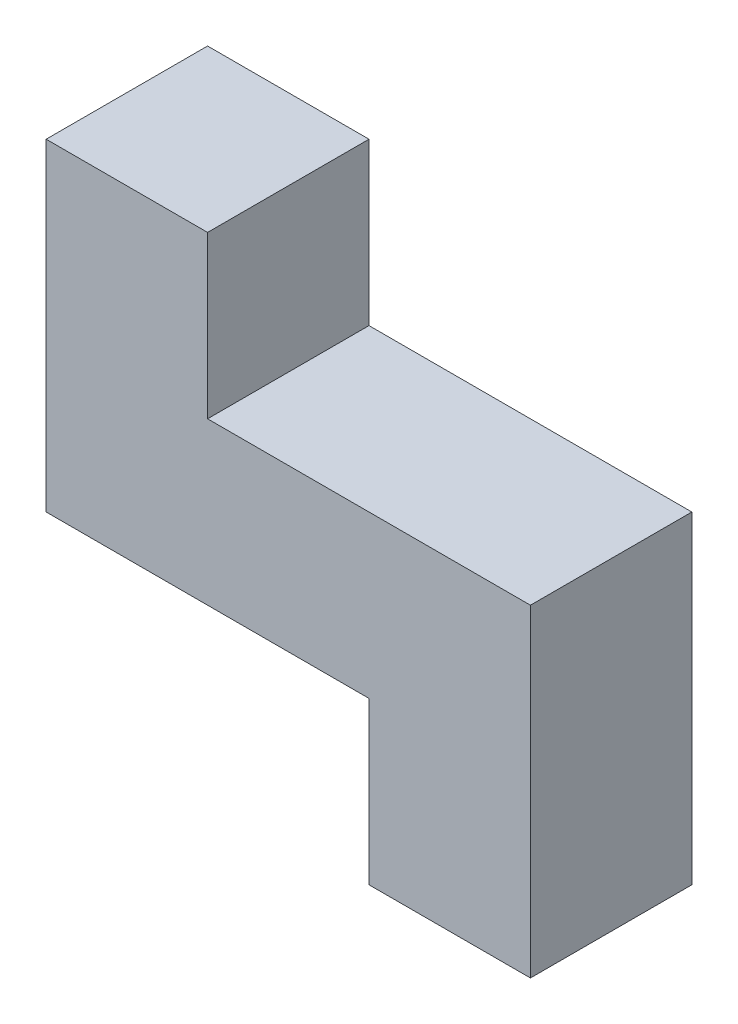
SolidWorks part; units mm, degrees
ref_plane "Front Plane" through (0, 0, 0) normal (0, 0, 1) x (1, 0, 0)
ref_plane "Top Plane" through (0, 0, 0) normal (0, 1, 0) x (1, 0, 0)
ref_plane "Right Plane" through (0, 0, 0) normal (1, 0, 0) x (0, 0, -1)
sketch "Sketch1" plane through (0, 0, 0) normal (0, 0, 1) x (1, 0, 0)
  line L58 (0, 76.2) -> (0, 25.4)
  line L59 (0, 25.4) -> (50.8, 25.4)
  line L60 (50.8, 25.4) -> (50.8, 0)
  line L61 (50.8, 0) -> (76.2, 0)
  line L62 (76.2, 0) -> (76.2, 50.8)
  line L63 (76.2, 50.8) -> (25.4, 50.8)
  line L64 (25.4, 50.8) -> (25.4, 76.2)
  line L65 (25.4, 76.2) -> (0, 76.2)
extrude "Boss-Extrude1" add sketch "Sketch1" along normal blind 25.4
